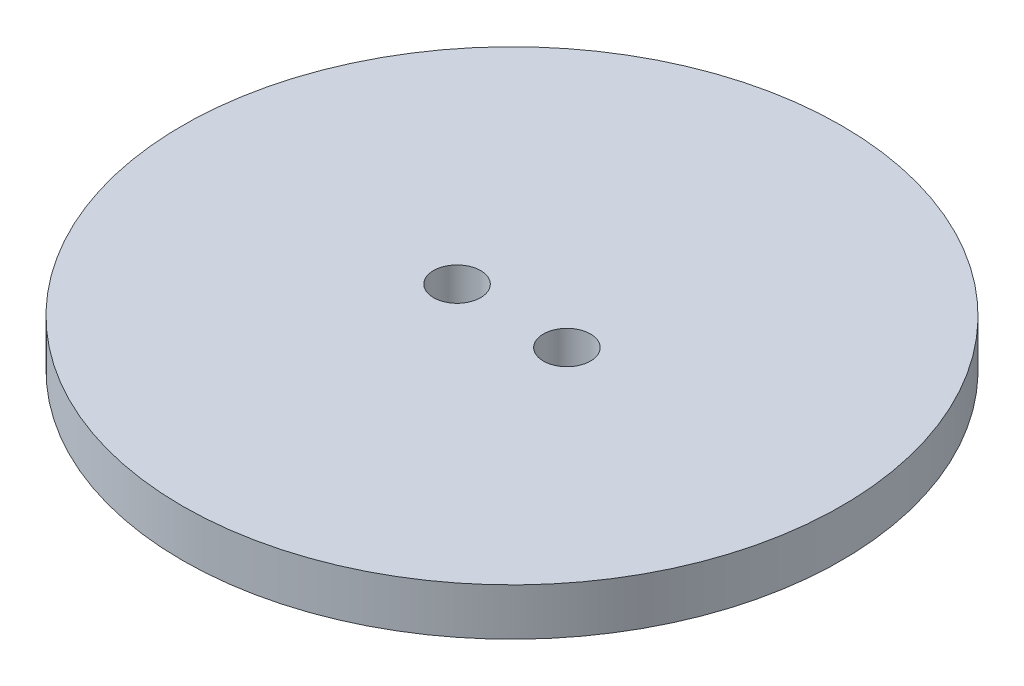
SolidWorks part; units mm, degrees
ref_plane "Plan de face" through (0, 0, 0) normal (0, 0, 1) x (1, 0, 0)
ref_plane "Plan de dessus" through (0, 0, 0) normal (0, 1, 0) x (1, 0, 0)
ref_plane "Plan de droite" through (0, 0, 0) normal (1, 0, 0) x (0, 0, -1)
sketch "Esquisse1" plane through (0, 0, 0) normal (0, 1, 0) x (1, 0, 0)
  line L0 (-3.5, 0) -> (0, 0) construction
  line L1 (2, 0) -> (3.5, 0) construction
  circle A0 centre (0, 0) radius 21
  circle A2 centre (-3.5, 0) radius 1.5
  circle A3 centre (3.5, 0) radius 1.5
  arc A10 (-1.9911, 2.8785) -> (-1.9911, -2.8785) centre (-3.5, 0) ccw construction
  circle A11 centre (0, 0) radius 6.9 construction
  circle A13 centre (0, 0) radius 16 construction
  circle A16 centre (0, 0) radius 22 construction
  dimension "D1" = 42
  dimension "D2" = 6.5
  dimension "D3" = 3.5
  dimension "D4" = 7
  dimension "D5" = 3
  dimension "D6" = 3
  dimension "D7" = 13.8
  dimension "D8" = 32
  dimension "D9" = 0
  dimension "D10" = 44
extrude "Boss.-Extru.1" add sketch "Esquisse1" along normal blind 3
